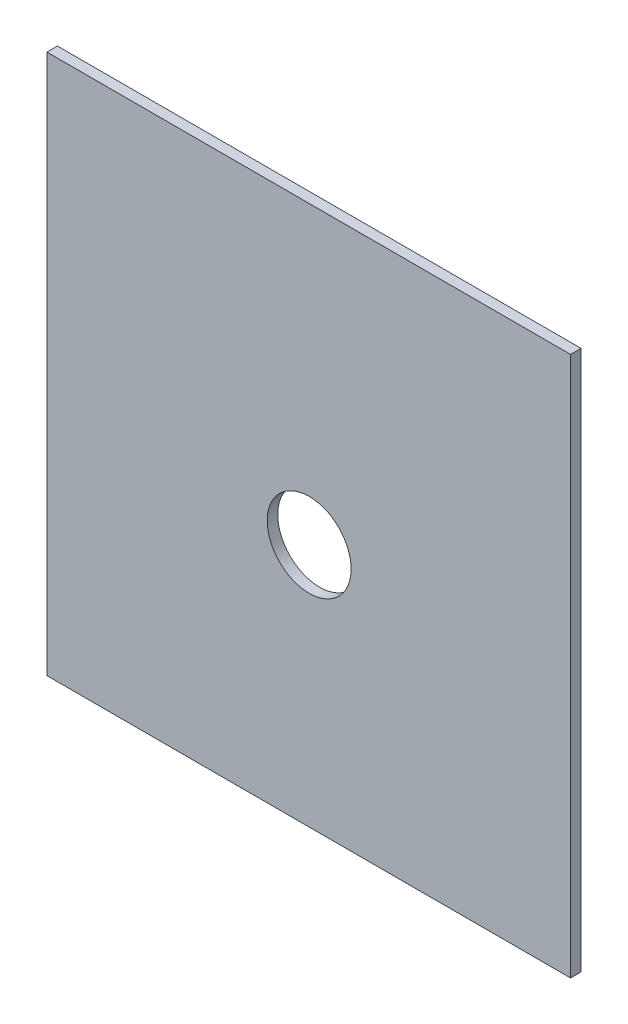
SolidWorks part; units mm, degrees
ref_plane "Front Plane" through (0, 0, 0) normal (0, 0, 1) x (1, 0, 0)
ref_plane "Top Plane" through (0, 0, 0) normal (0, 1, 0) x (1, 0, 0)
ref_plane "Right Plane" through (0, 0, 0) normal (1, 0, 0) x (0, 0, -1)
sketch "Sketch1" plane through (0, 0, 0) normal (0, 0, 1) x (1, 0, 0)
  line L0 (62.5, -257.4) -> (52.1484, -257.4) construction
  line L1 (0, 0) -> (249.6, 0)
  line L2 (0, 0) -> (0, -257.4)
  line L3 (0, -257.4) -> (249.6, -257.4)
  line L4 (249.6, 0) -> (249.6, -257.4)
  dimension "D2" = 249.6
extrude "Boss-Extrude1" add sketch "Sketch1" along normal blind 5
sketch "Sketch2" plane through (0, 0, 5) normal (0, 0, 1) x (1, 0, 0)
  line L0 (125, 0) -> (125, -350.4) construction
  circle A0 centre (125, -140.911) radius 20
  dimension "D1" = 40
extrude "Cut-Extrude1" cut sketch "Sketch2" against normal through all
